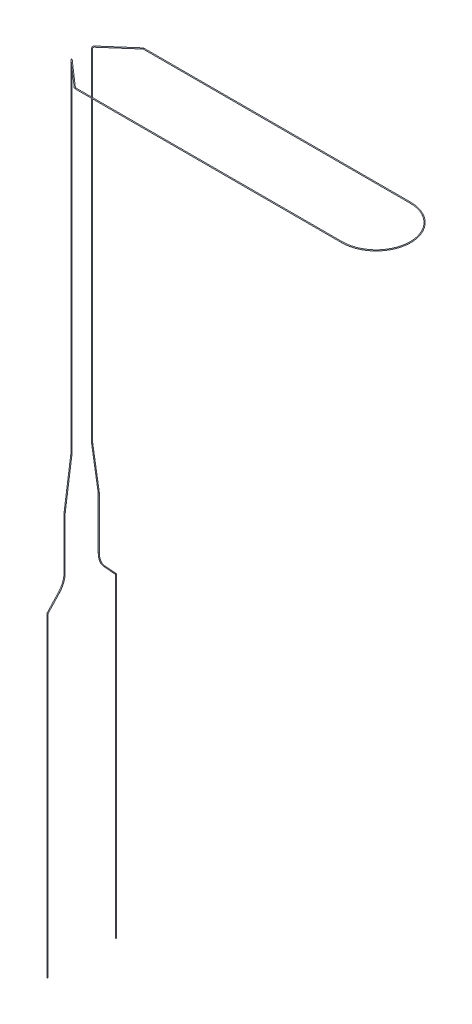
SolidWorks part; units mm, degrees
ref_plane "Plan de face" through (0, 0, 0) normal (0, 0, 1) x (1, 0, 0)
ref_plane "Plan de dessus" through (0, 0, 0) normal (0, 1, 0) x (1, 0, 0)
ref_plane "Plan de droite" through (0, 0, 0) normal (1, 0, 0) x (0, 0, -1)
sketch3d "Esquisse3D1"
  line L0 (0, 0, 0) -> (0, 0, 10.3571) construction
  line L6 (0, 257, 6) -> (0, 58.7107, 6)
  line L7 (0, 258, 6) -> (0, 258, 20) construction
  line L10 (0, 258, 20) -> (16, 258, 20) construction
  line L11 (0.7526, 258, 6.6585) -> (15.7172, 258, 19.7526)
  line L12 (0, 0, 0) -> (0, 258, 0) construction
  line L13 (16.3757, 258, 20) -> (172, 258, 20)
  line L14 (0, 258, 0) -> (219.9657, 258, 0) construction
  line L15 (0, 0, 5.3828) -> (0, -8.4495, 13.1824) construction
  line L16 (0, 0, 13.1824) -> (0, -8.4495, 13.1824) construction
  line L17 (0, -8.4495, 13.1824) -> (0, -15.5477, 19.7348)
  line L18 (0, 0, 10) -> (0, -0.31, 10)
  line L19 (0, -16.226, 20) -> (0, -200, 20)
  line L20 (0, 0, 10) -> (0, 29.2893, 10)
  line L21 (0, 30.7035, 9.8995) -> (0, 57.2965, 6.1005)
  line L22 (0, 0, -13.1824) -> (0, -8.4495, -13.1824) construction
  line L23 (0, 0, -5.3828) -> (0, -8.4495, -13.1824) construction
  line L24 (0, 258, -20) -> (16, 258, -20) construction
  line L25 (0, 258, -6) -> (0, 258, -20) construction
  line L26 (0, 30.7035, -9.8995) -> (0, 57.2965, -6.1005)
  line L27 (0, 0, -10) -> (0, 29.2893, -10)
  line L28 (0, -16.226, -20) -> (0, -200, -20)
  line L29 (0, 0, -10) -> (0, -0.31, -10)
  line L30 (0, -8.4495, -13.1824) -> (0, -15.5477, -19.7348)
  line L31 (16.3757, 258, -20) -> (172, 258, -20)
  line L32 (0.7526, 258, -6.6585) -> (15.7172, 258, -19.7526)
  line L33 (0, 257, -6) -> (0, 58.7107, -6)
  arc A0 (172, 258, 20) -> (172, 258, -20) centre (172, 258, 0) ccw
  circle A2 centre (20, 258, 20) radius 4 construction
  arc A3 (0, -0.31, 10) -> (0, -8.4495, 13.1824) centre (0, -0.31, 22) ccw
  arc A4 (16.3757, 258, 20) -> (15.7172, 258, 19.7526) centre (16.3757, 258, 19) ccw
  arc A5 (0, 29.2893, 10) -> (0, 30.7035, 9.8995) centre (0, 29.2893, 0) ccw
  arc A6 (0, -15.5477, 19.7348) -> (0, -16.226, 20) centre (0, -16.226, 19) ccw
  arc A7 (0, 58.7107, 6) -> (0, 57.2965, 6.1005) centre (0, 58.7107, 16) ccw
  arc A8 (0.7526, 258, 6.6585) -> (0, 257, 6) centre (0.7526, 257, 6.6585) ccw
  circle A9 centre (20, 258, -20) radius 4 construction
  arc A10 (0, 257, -6) -> (0.7526, 258, -6.6585) centre (0.7526, 257, -6.6585) cw
  arc A11 (0, 57.2965, -6.1005) -> (0, 58.7107, -6) centre (0, 58.7107, -16) cw
  arc A12 (0, -16.226, -20) -> (0, -15.5477, -19.7348) centre (0, -16.226, -19) cw
  arc A13 (0, 30.7035, -9.8995) -> (0, 29.2893, -10) centre (0, 29.2893, 0) cw
  arc A14 (15.7172, 258, -19.7526) -> (16.3757, 258, -20) centre (16.3757, 258, -19) cw
  arc A15 (0, -8.4495, -13.1824) -> (0, -0.31, -10) centre (0, -0.31, -22) cw
  point P13 (172, 278, 0)
  point P22 (20, 262, 20)
  point P25 (-12, -0.31, 22)
  point P28 (0, 30, 10)
  point P29 (16, 258, 20)
  point P31 (16.3757, 257, 19)
  point P34 (-10, 29.2893, 0)
  point P39 (0, -15.835, 20)
  point P40 (1, -16.226, 19)
  point P42 (0, 58, 6)
  point P44 (-10, 58.7107, 16)
  point P47 (0, 258, 6)
  point P48 (0.0941, 257, 7.4111)
  point P51 (20, 262, -20)
  point P61 (0.0941, 257, -7.4111)
  point P65 (-10, 58.7107, -16)
  point P69 (1, -16.226, -19)
  point P73 (-10, 29.2893, 0)
  point P77 (16.3757, 257, -19)
  point P80 (-12, -0.31, -22)
  point P83 (0, 58, -6)
  point P84 (0, -15.835, -20)
  point P85 (0, 30, -10)
  dimension "D3" = 20
  dimension "D4" = 8
  dimension "D8" = 12
  dimension "D12" = 1
  dimension "D15" = 10
  dimension "D16" = 10
  dimension "D17" = 1
  dimension "D2" = 20
  dimension "D5" = 172
  dimension "D13" = 30
  dimension "D6" = 6
  dimension "D7" = 47.29
  dimension "D9" = 20
  dimension "D10" = 0.31
  dimension "D11" = 200
  dimension "D14" = 200
  dimension "D18" = 258
  dimension "D19" = 10
sweep "Balayage1" add path "Esquisse3D1" circular profile diameter 0.5 parameters "D3"=0.5
